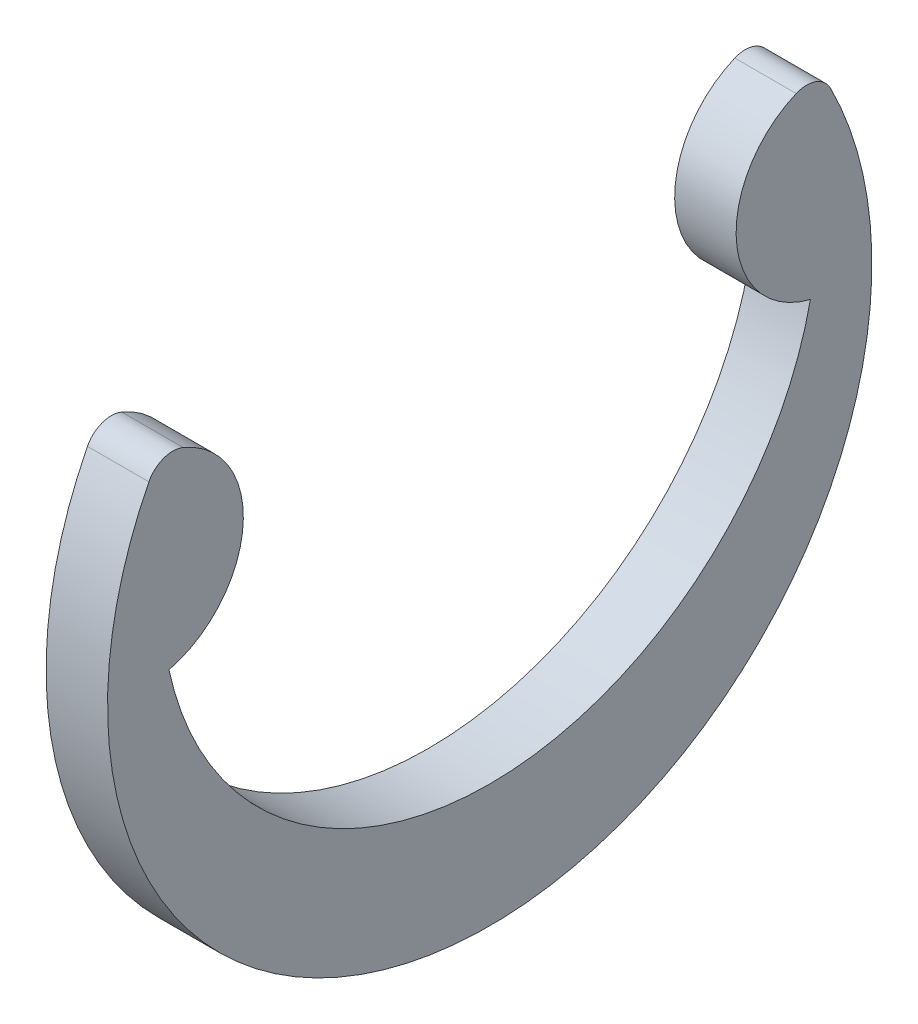
SolidWorks part; units mm, degrees
material "Cast Carbon Steel"
ref_plane "Front" through (0, 0, 0) normal (0, 0, 1) x (1, 0, 0)
ref_plane "Top" through (0, 0, 0) normal (0, 1, 0) x (1, 0, 0)
ref_plane "Right" through (0, 0, 0) normal (1, 0, 0) x (0, 0, -1)
sketch "Sketch1" plane through (0, 0, 0) normal (1, 0, 0) x (0, 0, -1)
  circle A0 centre (0, 0) radius 2.6797 construction
  arc A1 (-3.3147, 0) -> (3.3147, 0) centre (0, 0.7102) ccw
  circle A2 centre (0, 0) radius 3.9497 construction
  circle A3 centre (0, 0) radius 4.191 construction
  arc A4 (3.5226, 1.7865) -> (-3.5226, 1.7865) centre (0, 0) cw
  arc A5 (-3.1679, 1.9169) -> (-3.3147, 0) centre (-3.5593, 0.9828) cw
  arc A6 (-3.5226, 1.7865) -> (-3.1679, 1.9169) centre (-3.2751, 1.661) cw
  arc A7 (3.5226, 1.7865) -> (3.1679, 1.9169) centre (3.2751, 1.661) ccw
  arc A8 (3.3147, 0) -> (3.1679, 1.9169) centre (3.5593, 0.9828) cw
  arc A9 (3.1679, 1.9169) -> (3.3147, 0) centre (0, 0.7102) cw construction
  dimension "A" = 5.3594
  dimension "OD" = 7.8994
  dimension "D1" = 1.7865
  dimension "D2" = 6.6294
extrude "Extrude1" add sketch "Sketch1" along normal mid plane 0.635
sketch "Sketch2" plane through (0, 0, 0) normal (0, 0, 1) x (1, 0, 0)
  line L0 (-1.8415, 0) -> (5.5245, 0)
  line L1 (5.5245, 0) -> (5.5245, -3.175)
  line L3 (5.5245, -3.175) -> (0.3683, -3.175)
  line L4 (0.3683, -3.175) -> (0.3683, -2.794)
  line L5 (0.3683, -2.794) -> (-0.3683, -2.794)
  line L6 (-0.3683, -2.794) -> (-0.3683, -3.175)
  line L7 (-0.3683, -3.175) -> (-1.8415, -3.175) construction
  line L8 (-1.8415, -3.175) -> (-1.8415, 0) construction
  line L9 (0, -2.794) -> (0, 0) construction
  line L10 (5.5245, 0) -> (14.0551, 0) construction
  line L11 (-0.3683, -3.175) -> (-1.651, -3.175)
  line L12 (-1.651, -3.175) -> (-1.8415, -2.9845)
  line L13 (-1.8415, -2.9845) -> (-1.8415, 0)
  point P14 (-0.3683, -2.9845)
  dimension "D2" = 7.366
  dimension "D3" = 1.8415
  dimension "D4" = 45
revolve "Revolve1" [suppressed] add sketch "Sketch2" angle 360 about L10
equation "\"D2@Sketch2\" = \"W@Sketch2\"*10"
equation "\"D3@Sketch2\" = \"D2@Sketch2\"/4"
equation "\"D1@Sketch1\" = \"A@Sketch1\"/3"
equation "\"D2@Sketch1\" = (\"OD@Sketch1\"+\"A@Sketch1\")/2"
